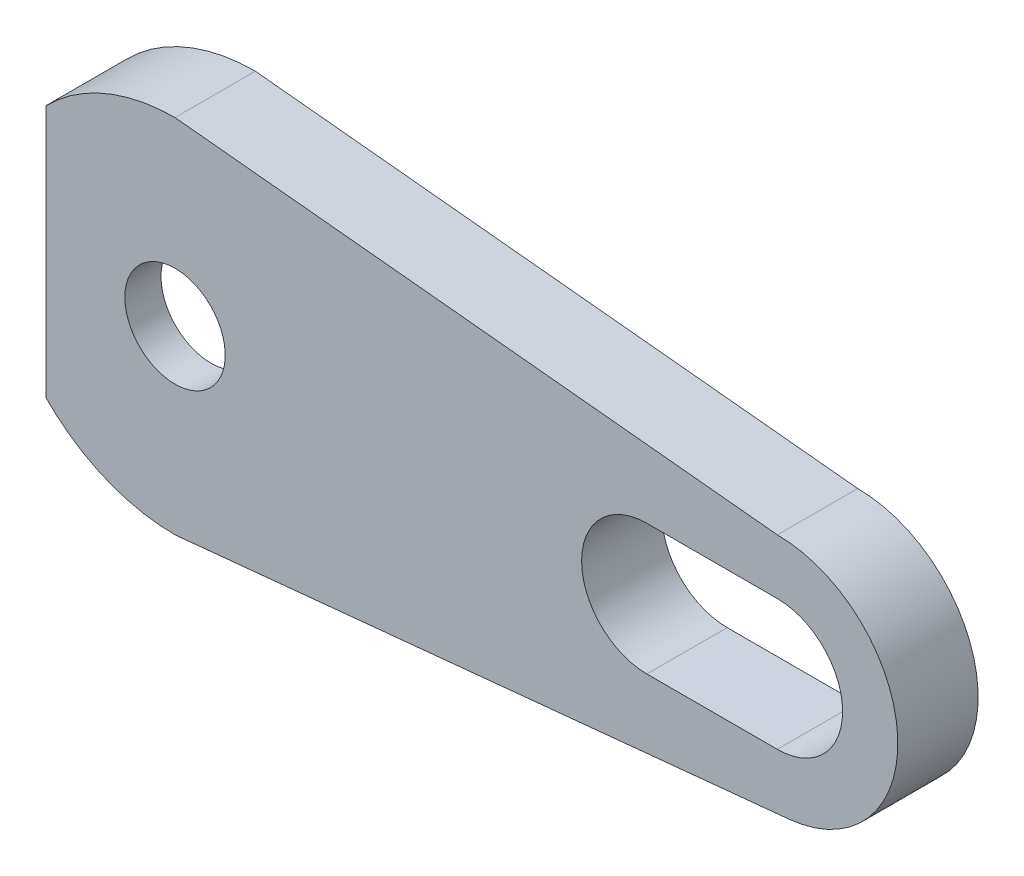
SolidWorks part; units mm, degrees
ref_plane "Front Plane" through (0, 0, 0) normal (0, 0, 1) x (1, 0, 0)
ref_plane "Top Plane" through (0, 0, 0) normal (0, 1, 0) x (1, 0, 0)
ref_plane "Right Plane" through (0, 0, 0) normal (1, 0, 0) x (0, 0, -1)
sketch "Esquisse1" plane through (0, 0, 0) normal (0, 0, 1) x (1, 0, 0)
  line L0 (-4.3758, 4.25) -> (-6.4265, 6.3008)
  line L1 (4.3758, 4.25) -> (17.3156, 2.7822)
  line L2 (17.3156, -2.7822) -> (4.3758, -4.25)
  line L3 (23.5, 3.25) -> (30, 3.25)
  line L4 (0, 9) -> (30, 6)
  line L5 (0, -9) -> (30.5912, -5.9708)
  line L6 (-4.3758, -4.25) -> (-6.4265, -6.3008)
  line L7 (23.5, -3.25) -> (30, -3.25)
  arc A0 (4.3758, 4.25) -> (-4.3758, 4.25) centre (0, 0) ccw
  arc A1 (17.3156, -2.7822) -> (17.3156, 2.7822) centre (17, 0) ccw
  arc A2 (4.3758, -4.25) -> (-4.3758, -4.25) centre (0, 0) cw
  arc A3 (-6.4265, 6.3008) -> (0, 9) centre (0, 0) cw
  arc A4 (30, 3.25) -> (30, -3.25) centre (30, 0) cw
  arc A5 (-6.4265, -6.3008) -> (0, -9) centre (0, 0) ccw
  arc A6 (30, 6) -> (30.5912, -5.9708) centre (30, 0) cw
  arc A7 (23.5, 3.25) -> (23.5, -3.25) centre (23.5, 0) ccw
  dimension "D2" = 6.1
  dimension "D3" = 2.8
  dimension "D5" = 3.25
  dimension "D6" = 9
  dimension "D8" = 30
  dimension "D1" = 8.5
  dimension "D4" = 17
  dimension "D7" = 23.5
  dimension "D9" = 6
  dimension "D10" = 6.5
extrude "Main" add sketch "Esquisse1" along normal blind 4
sketch "Esquisse2" plane through (0, 0, 4) normal (0, 0, -1) x (-1, 0, 0)
  line L0 (0, -9) -> (-13.3031, -7.6827)
  line L1 (0, -9) -> (-30.5912, -5.9708) construction
  line L2 (0, -9) -> (-30.5912, -5.9708) construction
  line L3 (0, 9) -> (-13.3031, 7.6697)
  line L4 (6.4265, -6.3008) -> (6.4265, 6.3008)
  line L5 (-30, 6) -> (0, 9) construction
  line L6 (-30, 6) -> (0, 9) construction
  line L7 (0, -9) -> (-30.5912, -5.9708) construction
  line L10 (6.4265, 6.3008) -> (4.3758, 4.25) construction
  arc A0 (6.4265, 6.3008) -> (0, 9) centre (0, 0) ccw construction
  arc A1 (0, -9) -> (6.4265, -6.3008) centre (0, 0) ccw
  circle A2 centre (0, 0) radius 2.5
  arc A3 (6.4265, 6.3008) -> (0, 9) centre (0, 0) ccw
  arc A4 (-13.3031, -7.6827) -> (-13.3031, 7.6697) centre (-12.5355, -0.0065) cw
  arc A5 (-23.5, -3.25) -> (-23.5, 3.25) centre (-23.5, 0) ccw construction
  arc A6 (0, -9) -> (6.4265, -6.3008) centre (0, 0) ccw construction
  point P6 (-17.0358, 6.3008)
  point P21 (-9.6964, -6.3899)
  point P22 (-14.9919, 16.9797)
  point P24 (-12.6987, -16.1983)
  point P31 (-20.1308, 6.3159)
  point P32 (-20.469, -5.5128)
  point P33 (-17.0918, -6.7458)
  point P36 (-13.8443, 7.1541)
  dimension "D1" = 5
extrude "Boss-Extrude1" add sketch "Esquisse2" along normal blind 1.8
